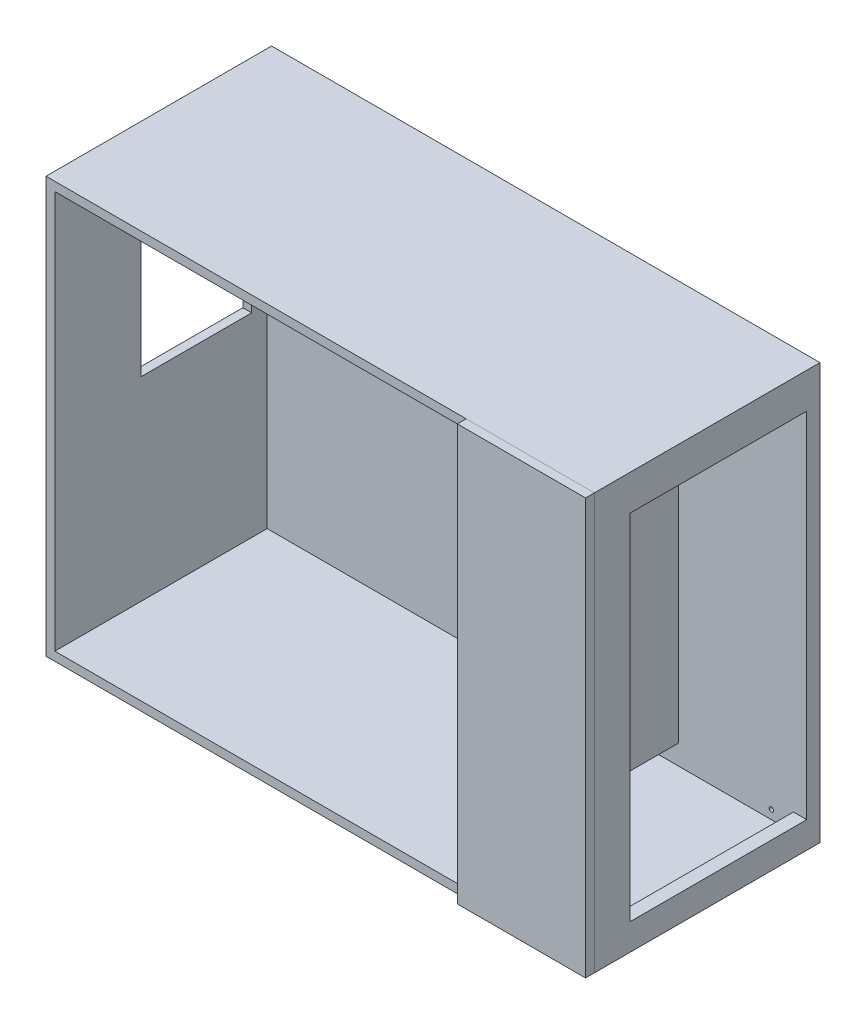
SolidWorks part; units mm, degrees
ref_plane "Front Plane" through (0, 0, 0) normal (0, 0, 1) x (1, 0, 0)
ref_plane "Top Plane" through (0, 0, 0) normal (0, 1, 0) x (1, 0, 0)
ref_plane "Right Plane" through (0, 0, 0) normal (1, 0, 0) x (0, 0, -1)
sketch "Croquis1" plane through (0, 0, 0) normal (0, 1, 0) x (1, 0, 0)
  line L1 (-650, -255) -> (650, -255)
  line L2 (-650, -255) -> (-650, 255)
  line L3 (-650, 255) -> (650, 255)
  line L4 (650, -255) -> (650, 255)
  point P4 (0, 255)
  point P6 (650, 0)
  dimension "D1" = 1300
  dimension "D2" = 510
extrude "Saliente-Extruir1" add sketch "Croquis1" along normal blind 1200
sketch "Croquis2" plane through (0, 0, 255) normal (0, 0, 1) x (1, 0, 0)
  line L6 (-630, 1010) -> (-630, 110)
  line L7 (-650, 1200) -> (-650, 0) construction
  line L11 (-630, 1010) -> (280, 1010)
  line L12 (-650, 1200) -> (650, 1200) construction
  line L13 (-630, 110) -> (280, 110)
  line L14 (280, 110) -> (280, 1010)
  line L15 (-650, 0) -> (650, 0) construction
  line L16 (650, 1200) -> (650, 0) construction
  line L17 (-630, 110) -> (-650, 110)
  line L18 (-630, 1010) -> (-650, 1010)
  line L19 (-650, 1010) -> (-650, 110)
  dimension "D1" = 20
  dimension "D2" = 190
  dimension "D3" = 110
  dimension "D4" = 370
extrude "Cortar-Extruir1" cut sketch "Croquis2" against normal blind 480 contours L13 L14 L11 L6
sketch "Croquis3" plane through (-650, 0, 0) normal (-1, 0, 0) x (0, 0, 1)
  line L0 (60, 950) -> (-190, 950)
  line L1 (60, 950) -> (60, 550)
  line L2 (60, 550) -> (-190, 550)
  line L3 (-190, 950) -> (-190, 550)
  line L4 (-255, 1200) -> (-255, 0) construction
  line L5 (-255, 1200) -> (255, 1200) construction
  dimension "D1" = 400
  dimension "D2" = 65
  dimension "D3" = 250
  dimension "D4" = 250
extrude "Cortar-Extruir2" cut sketch "Croquis3" against normal blind 70
sketch "Croquis4" plane through (0, 0, 255) normal (0, 0, 1) x (1, 0, 0)
  line L0 (-650, 1200) -> (650, 1200) construction
  line L1 (560, 110) -> (300, 110)
  line L2 (560, 110) -> (560, 1010)
  line L3 (560, 1010) -> (300, 1010)
  line L4 (300, 110) -> (300, 1010)
  line L5 (560, 110) -> (300, 1010) construction
  line L6 (560, 1010) -> (300, 110) construction
  line L7 (650, 1200) -> (650, 0) construction
  line L8 (280, 110) -> (280, 1010) construction
  line L9 (-650, 0) -> (650, 0) construction
  point P0 (430, 560)
  dimension "D1" = 190
  dimension "D2" = 90
  dimension "D3" = 20
  dimension "D4" = 110
extrude "Cortar-Extruir3" cut sketch "Croquis4" against normal blind 480
sketch "Croquis5" plane through (650, 0, 0) normal (1, 0, 0) x (0, 0, -1)
  line L0 (-255, 0) -> (255, 0) construction
  line L1 (-175, 950) -> (225, 950)
  line L2 (-175, 950) -> (-175, 150)
  line L3 (-175, 150) -> (225, 150)
  line L4 (225, 950) -> (225, 150)
  line L5 (-175, 950) -> (225, 150) construction
  line L6 (-175, 150) -> (225, 950) construction
  line L7 (-255, 1200) -> (-255, 0) construction
  point P0 (25, 550)
  dimension "D1" = 400
  dimension "D2" = 800
  dimension "D3" = 150
  dimension "D4" = 80
extrude "Cortar-Extruir4" cut sketch "Croquis5" against normal blind 320
sketch "Croquis6" plane through (280, 0, 0) normal (-1, 0, 0) x (0, 0, 1)
  line L0 (-225, 110) -> (-225, 1010) construction
  line L1 (-225, 110) -> (-95, 110)
  line L2 (-225, 110) -> (-225, 155)
  line L3 (-225, 155) -> (-95, 155)
  line L4 (-95, 110) -> (-95, 155)
  line L5 (-225, 110) -> (-95, 155) construction
  line L6 (-225, 155) -> (-95, 110) construction
  line L7 (-225, 110) -> (255, 110) construction
  point P0 (-160, 132.5)
  dimension "D1" = 130
  dimension "D2" = 45
  dimension "D3" = 0
  dimension "D4" = 0
extrude "Cortar-Extruir5" cut sketch "Croquis6" against normal blind 230
sketch "Croquis7" plane through (0, 0, 255) normal (0, 0, 1) x (1, 0, 0)
  line L0 (300, 1200) -> (650, 1200)
  line L1 (-650, 1200) -> (650, 1200) construction
  line L2 (650, 1200) -> (650, 0)
  line L3 (650, 0) -> (300, 0)
  line L4 (-650, 0) -> (650, 0) construction
  line L10 (300, 1200) -> (300, 0)
  dimension "D1" = 350
extrude "Saliente-Extruir2" add sketch "Croquis7" along normal blind 20 separate body
sketch "Croquis9" plane through (-650, 0, 0) normal (-1, 0, 0) x (0, 0, 1)
  line L0 (255, 1200) -> (255, 0) construction
  line L1 (-255, 0) -> (255, 0)
  line L2 (-255, 0) -> (-255, 90)
  line L3 (-255, 90) -> (255, 90)
  line L4 (255, 0) -> (255, 90)
  dimension "D1" = 90
extrude "Cortar-Extruir6" cut sketch "Croquis9" against normal blind 1440
sketch "Croquis11" plane through (0, 0, 275) normal (0, 0, 1) x (1, 0, 0)
  line L0 (650, 0) -> (300, 0) construction
  line L1 (300, 1200) -> (590, 1200)
  line L2 (300, 1200) -> (300, 0)
  line L3 (300, 0) -> (590, 0)
  line L4 (590, 1200) -> (590, 0)
  line L5 (650, 1200) -> (650, 0) construction
  line L6 (590, 1200) -> (650, 1200)
  line L7 (650, 1200) -> (650, 0)
  line L8 (650, 0) -> (590, 0)
  line L9 (300, 90) -> (590, 90)
  line M3 (650, 1200) -> (300, 1200)
  line M5 (300, 0) -> (650, 0)
  line M6 (650, 0) -> (650, 1200)
  dimension "D1" = 60
  dimension "D2" = 90
extrude "Cortar-Extruir7" cut sketch "Croquis11" against normal blind 1440 contours L4 M3 M5 M6
sketch "Croquis12" plane through (0, 0, 275) normal (0, 0, 1) x (1, 0, 0)
  line L0 (590, 1200) -> (590, 0) construction
  line L1 (300, 0) -> (590, 0)
  line L2 (300, 0) -> (300, 90)
  line L3 (300, 90) -> (590, 90)
  line L4 (590, 0) -> (590, 90)
  dimension "D1" = 90
extrude "Cortar-Extruir8" cut sketch "Croquis12" against normal blind 1440
ref_plane "Plano1" through (-650, 1200, 255) normal (1, 0, 0) x (0, 0, -1)
sketch "Croquis14" plane through (0, 0, 255) normal (0, 0, 1) x (1, 0, 0)
  line L1 (-650, 1200) -> (653.3612, 1200)
  line L2 (-650, 1200) -> (-650, 1030)
  line L3 (-650, 1030) -> (653.3612, 1030)
  line L4 (653.3612, 1200) -> (653.3612, 1030)
  dimension "D1" = 170
extrude "Cortar-Extruir9" cut sketch "Croquis14" against normal blind 1440
sketch "Croquis15" plane through (0, 0, 275) normal (0, 0, 1) x (1, 0, 0)
  line L0 (590, 1200) -> (590, 90) construction
  line L1 (300, 1200) -> (590, 1200)
  line L2 (300, 1200) -> (300, 1130)
  line L3 (300, 1130) -> (590, 1130)
  line L4 (590, 1200) -> (590, 1130)
  dimension "D1" = 70
extrude "Cortar-Extruir10" cut sketch "Croquis15" against normal blind 1440
sketch "Croquis16" plane through (0, 0, 275) normal (0, 0, 1) x (1, 0, 0)
  line L0 (590, 1130) -> (590, 90) construction
  line L1 (300, 1130) -> (590, 1130)
  line L2 (300, 1130) -> (300, 1030)
  line L3 (300, 1030) -> (590, 1030)
  line L4 (590, 1130) -> (590, 1030)
  dimension "D1" = 100
extrude "Cortar-Extruir11" cut sketch "Croquis16" against normal blind 1440
sketch "Croquis17" plane through (0, 0, -255) normal (0, 0, -1) x (-1, 0, 0)
  line L0 (-590, 90) -> (650, 90) construction
  line L1 (-590, 1030) -> (-590, 90) construction
  circle A0 centre (-510, 130) radius 5
  dimension "D3" = 10
  dimension "D1" = 40
  dimension "D2" = 80
extrude "Cortar-Extruir12" cut sketch "Croquis17" against normal blind 30
